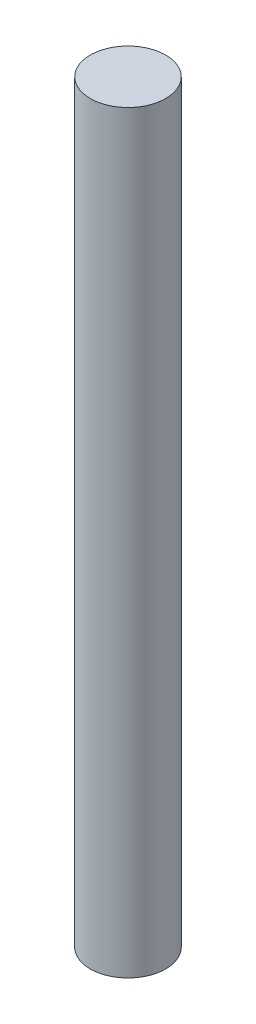
SolidWorks part; units mm, degrees
ref_plane "Front Plane" through (0, 0, 0) normal (0, 0, 1) x (1, 0, 0)
ref_plane "Top Plane" through (0, 0, 0) normal (0, 1, 0) x (1, 0, 0)
ref_plane "Right Plane" through (0, 0, 0) normal (1, 0, 0) x (0, 0, -1)
sketch "Sketch1" plane through (0, 0, 0) normal (0, 1, 0) x (1, 0, 0)
  circle A0 centre (0, 0) radius 25
extrude "Boss-Extrude1" add sketch "Sketch1" along normal blind 500
